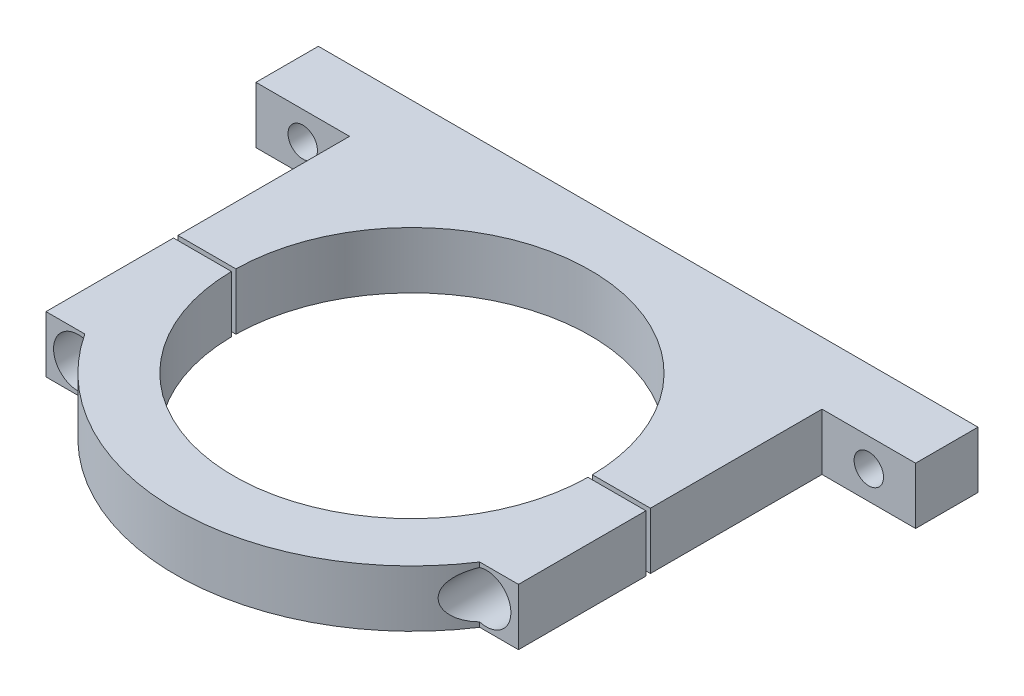
SolidWorks part; units mm, degrees
ref_plane "Front Plane" through (0, 0, 0) normal (0, 0, 1) x (1, 0, 0)
ref_plane "Top Plane" through (0, 0, 0) normal (0, 1, 0) x (1, 0, 0)
ref_plane "Right Plane" through (0, 0, 0) normal (1, 0, 0) x (0, 0, -1)
sketch "Sketch1" plane through (0, 0, 0) normal (0, 1, 0) x (1, 0, 0)
  line L0 (0, 0) -> (0, 53) construction
  line L1 (-74, 53) -> (74, 53)
  line L2 (74, 53) -> (74, 39)
  line L3 (74, 39) -> (53, 39)
  line L4 (53, 39) -> (53, 0)
  line L5 (-74, 53) -> (-74, 39)
  line L6 (-74, 39) -> (-53, 39)
  line L7 (-53, 39) -> (-53, 0)
  line L8 (-53, 39) -> (53, 39) construction
  line L9 (0, 0) -> (0, -29.1) construction
  line L10 (53, 0) -> (53, -29.1)
  line L11 (53, -29.1) -> (44.2966, -29.1)
  line L12 (-53, -29.1) -> (-53, 0)
  line L13 (27.4443, -29.1) -> (-27.4443, -29.1) construction
  line L14 (-44.2966, -29.1) -> (-53, -29.1)
  circle A0 centre (0, 0) radius 40
  arc A1 (-44.2966, -29.1) -> (44.2966, -29.1) centre (0, 0) ccw
  dimension "D1" = 80
  dimension "D2" = 106
  dimension "D3" = 53
  dimension "D4" = 148
  dimension "D5" = 14
  dimension "D6" = 29.1
extrude "Boss-Extrude1" add sketch "Sketch1" along normal blind 12.7
sketch "Sketch3" plane through (0, 0, -39) normal (0, 0, 1) x (1, 0, 0)
  line L0 (74, 12.7) -> (53, 0) construction
  line L1 (-53, 12.7) -> (-74, 0) construction
  circle A0 centre (-63.5, 6.35) radius 3.3
  circle A1 centre (63.5, 6.35) radius 3.3
  dimension "D1" = 6.6
extrude "Cut-Extrude2" cut sketch "Sketch3" against normal through all
sketch "Sketch4" plane through (0, 0, 0) normal (0, 0, 1) x (1, 0, 0)
  line L0 (-53, 6.35) -> (53, 6.35) construction
  line L1 (-53, 12.7) -> (-53, 0) construction
  line L2 (53, 12.7) -> (53, 0) construction
  circle A0 centre (45.8, 6.35) radius 3.3
  circle A1 centre (-45.8, 6.35) radius 3.3
  dimension "D1" = 6.6
  dimension "D2" = 7.2
  dimension "D3" = 7.2
extrude "Cut-Extrude3" cut sketch "Sketch4" against normal blind 12.7 and the other way blind 72.7
sketch "Sketch2" plane through (0, 12.7, 0) normal (0, 1, 0) x (1, 0, 0)
  line L1 (76.8529, -0.5) -> (-76.8529, -0.5)
  line L2 (76.8529, -0.5) -> (76.8529, 0.5)
  line L3 (76.8529, 0.5) -> (-76.8529, 0.5)
  line L4 (-76.8529, -0.5) -> (-76.8529, 0.5)
  line L5 (76.8529, -0.5) -> (-76.8529, 0.5) construction
  line L6 (76.8529, 0.5) -> (-76.8529, -0.5) construction
  point P0 (0, 0)
  dimension "D1" = 1
  dimension "D2" = 153.7058
extrude "Cut-Extrude1" cut sketch "Sketch2" against normal through all both and the other way through all
sketch "Sketch5" plane through (0, 0, 0) normal (0, 0, 1) x (1, 0, 0)
  circle A0 centre (45.8, 6.35) radius 5.5
  circle A1 centre (-45.8, 6.35) radius 5.5
  dimension "D1" = 11
extrude "Cut-Extrude4" cut sketch "Sketch5" against normal blind 18.7 from offset 40
